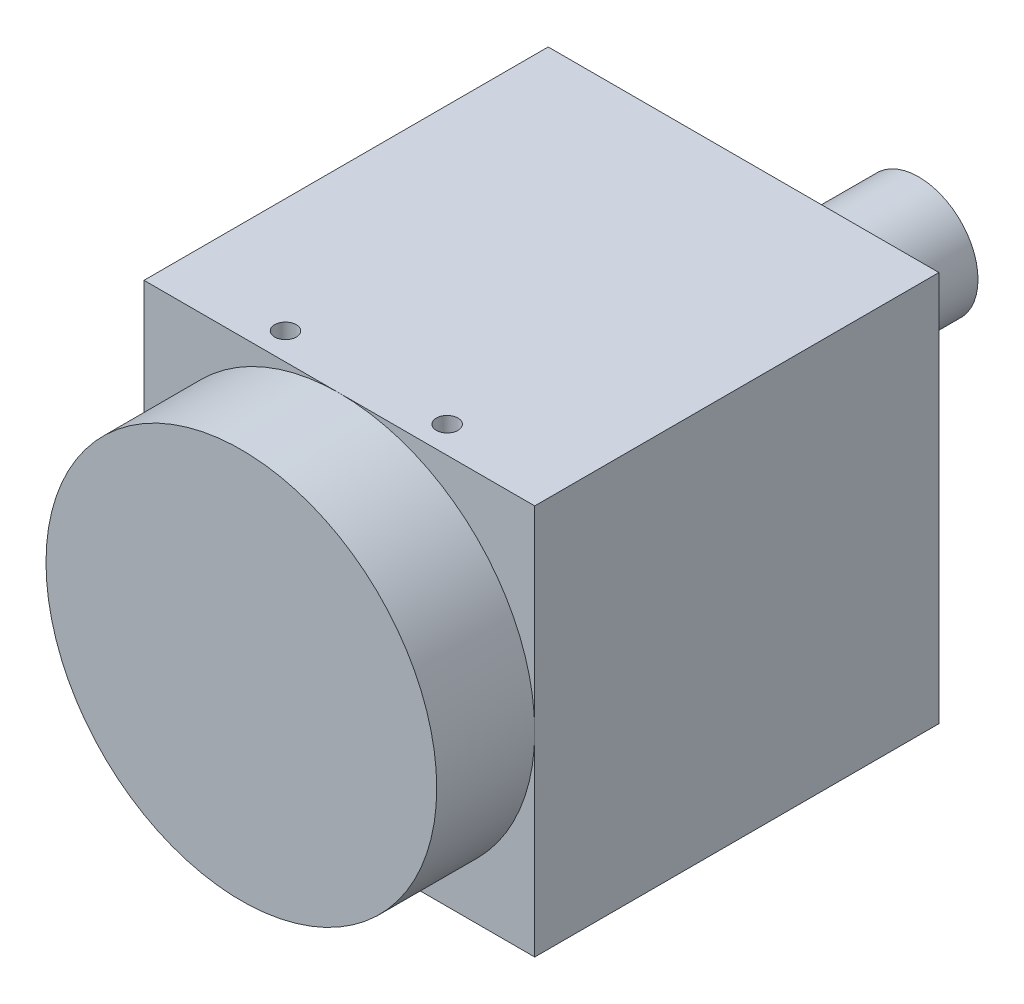
SolidWorks part; units mm, degrees
ref_plane "Front Plane" through (0, 0, 0) normal (0, 0, 1) x (1, 0, 0)
ref_plane "Top Plane" through (0, 0, 0) normal (0, 1, 0) x (1, 0, 0)
ref_plane "Right Plane" through (0, 0, 0) normal (1, 0, 0) x (0, 0, -1)
sketch "Sketch1" plane through (0, 0, 0) normal (0, 0, 1) x (1, 0, 0)
  line L1 (-14.5, 14.5) -> (14.5, 14.5)
  line L2 (-14.5, 14.5) -> (-14.5, -14.5)
  line L3 (-14.5, -14.5) -> (14.5, -14.5)
  line L4 (14.5, 14.5) -> (14.5, -14.5)
  line L5 (-14.5, 14.5) -> (14.5, -14.5) construction
  line L6 (-14.5, -14.5) -> (14.5, 14.5) construction
  point P0 (0, 0)
  dimension "D1" = 29
extrude "Boss-Extrude1" add sketch "Sketch1" along normal mid plane 30
sketch "Sketch2" plane through (0, 0, 15) normal (0, 0, 1) x (1, 0, 0)
  line L0 (14.5, -14.5) -> (14.5, 14.5) construction
  circle A0 centre (0, 0) radius 14.5
extrude "Boss-Extrude2" add sketch "Sketch2" along normal blind 7.274
sketch "Sketch3" plane through (0, 14.5, 0) normal (0, 1, 0) x (1, 0, 0)
  line L0 (-6, -13) -> (6, -13) construction
  line L1 (0, -15) -> (-14.5, -15) construction
  point P0 (-6, -13)
  point P1 (6, -13)
  point P4 (0, -13)
  dimension "D1" = 2
  dimension "D2" = 12
hole_wizard "M2x0.4 Tapped Hole1" positions "3DSketch1" profile "Sketch4" tap size "M2x0.4" standard "ANSI Metric"
sketch3d "3DSketch1"
  point P0 (-6, 14.5, 13)
  point P3 (6, 14.5, 13)
sketch "Sketch4" plane through (-6, 14.5, 13) normal (1, 0, 0) x (0, 0, 1)
  line L0 (0, 0) -> (0, 2.9807)
  line L1 (0, 2.9807) -> (0.8, 2.5)
  line L2 (0.8, 2.5) -> (0.8, 0)
  line L5 (0.8, 0) -> (0, 0)
  line L10 (0, 2.9807) -> (-0.8, 2.5) construction
  line L11 (0, -6.35) -> (0, 107.95) construction
  dimension "Tap Drill Dia." = 1.6
  dimension "Tap Drill Depth" = 2.5
  dimension "Drill Angle" = 118
cosmetic thread "Hole Thread1" parameters "D1"=2.5, "D2"=2
cosmetic thread "Hole Thread2" parameters "D1"=2.5, "D2"=2
sketch "Sketch5" plane through (0, -14.5, 0) normal (0, -1, 0) x (1, 0, 0)
  line L0 (0, 15) -> (0, -15) construction
  line L1 (-14.5, -15) -> (14.5, -15) construction
  line L2 (0, 15) -> (14.5, 15) construction
  line L3 (14.5, 15) -> (0, 15) construction
  point P5 (10, 12)
  point P6 (6, 10.5)
  point P7 (0, -11.7)
  point P8 (6, -11.7)
  point P15 (-6, -11.7)
  point P16 (-6, 10.5)
  point P17 (-10, 12)
  dimension "D1" = 6
  dimension "D2" = 10
  dimension "D3" = 23.7
  dimension "D4" = 4.5
  dimension "D5" = 3
hole_wizard "M2x0.4 Tapped Hole2" positions "3DSketch2" profile "Sketch6" tap size "M2x0.4" standard "ANSI Metric"
sketch3d "3DSketch2"
  point P6 (-6, -14.5, -11.7)
  point P9 (6, -14.5, -11.7)
sketch "Sketch6" plane through (-6, -14.5, -11.7) normal (1, 0, 0) x (0, 0, -1)
  line L0 (0, 0) -> (0, 2.4807)
  line L1 (0, 2.4807) -> (0.8, 2)
  line L2 (0.8, 2) -> (0.8, 0)
  line L5 (0.8, 0) -> (0, 0)
  line L10 (0, 2.4807) -> (-0.8, 2) construction
  line L11 (0, -6.35) -> (0, 107.95) construction
  dimension "Tap Drill Dia." = 1.6
  dimension "Tap Drill Depth" = 2
  dimension "Drill Angle" = 118
cosmetic thread "Hole Thread3" parameters "D1"=2, "D2"=2
cosmetic thread "Hole Thread4" parameters "D1"=2, "D2"=2
hole_wizard "M2x0.4 Tapped Hole3" positions "3DSketch3" profile "Sketch7" tap size "M2x0.4" standard "ANSI Metric"
sketch3d "3DSketch3"
  point P0 (-6, -14.5, 10.5)
  point P3 (6, -14.5, 10.5)
sketch "Sketch7" plane through (-6, -14.5, 10.5) normal (1, 0, 0) x (0, 0, -1)
  line L0 (0, 0) -> (0, 2.9807)
  line L1 (0, 2.9807) -> (0.8, 2.5)
  line L2 (0.8, 2.5) -> (0.8, 0)
  line L5 (0.8, 0) -> (0, 0)
  line L10 (0, 2.9807) -> (-0.8, 2.5) construction
  line L11 (0, -6.35) -> (0, 107.95) construction
  dimension "Tap Drill Dia." = 1.6
  dimension "Tap Drill Depth" = 2.5
  dimension "Drill Angle" = 118
cosmetic thread "Hole Thread5" parameters "D1"=2.5, "D2"=2
cosmetic thread "Hole Thread6" parameters "D1"=2.5, "D2"=2
hole_wizard "M3x0.5 Tapped Hole2" positions "3DSketch4" profile "Sketch8" tap size "M3x0.5" standard "ANSI Metric"
sketch3d "3DSketch4"
  point P0 (10, -14.5, 12)
  point P3 (-10, -14.5, 12)
sketch "Sketch8" plane through (10, -14.5, 12) normal (1, 0, 0) x (0, 0, -1)
  line L0 (0, 0) -> (0, 3.5511)
  line L1 (0, 3.5511) -> (1.25, 2.8)
  line L2 (1.25, 2.8) -> (1.25, 0)
  line L5 (1.25, 0) -> (0, 0)
  line L10 (0, 3.5511) -> (-1.25, 2.8) construction
  line L11 (0, -6.35) -> (0, 107.95) construction
  dimension "Tap Drill Dia." = 2.5
  dimension "Tap Drill Depth" = 2.8
  dimension "Drill Angle" = 118
cosmetic thread "Hole Thread7" parameters "D1"=2.8, "D2"=3
cosmetic thread "Hole Thread8" parameters "D1"=2.8, "D2"=3
hole_wizard "M3x0.5 Tapped Hole1" positions "3DSketch5" profile "Sketch9" tap size "M3x0.5" standard "ANSI Metric"
sketch3d "3DSketch5"
  point P6 (0, -14.5, -11.7)
sketch "Sketch9" plane through (0, -14.5, -11.7) normal (1, 0, 0) x (0, 0, -1)
  line L0 (0, 0) -> (0, 3.2511)
  line L1 (0, 3.2511) -> (1.25, 2.5)
  line L2 (1.25, 2.5) -> (1.25, 0)
  line L5 (1.25, 0) -> (0, 0)
  line L10 (0, 3.2511) -> (-1.25, 2.5) construction
  line L11 (0, -6.35) -> (0, 107.95) construction
  dimension "Tap Drill Dia." = 2.5
  dimension "Tap Drill Depth" = 2.5
  dimension "Drill Angle" = 118
cosmetic thread "Hole Thread9" parameters "D1"=2.5, "D2"=3
sketch "Sketch10" plane through (0, 0, -15) normal (0, 0, -1) x (-1, 0, 0)
  line L0 (-14.5, -14.5) -> (-14.5, 14.5) construction
  line L1 (-14.5, 14.5) -> (14.5, 14.5) construction
  circle A0 centre (-6.5, 9) radius 4.4
  dimension "D2" = 8.8
  dimension "D1" = 8
  dimension "D3" = 5.5
extrude "Boss-Extrude3" add sketch "Sketch10" along normal blind 6.5
